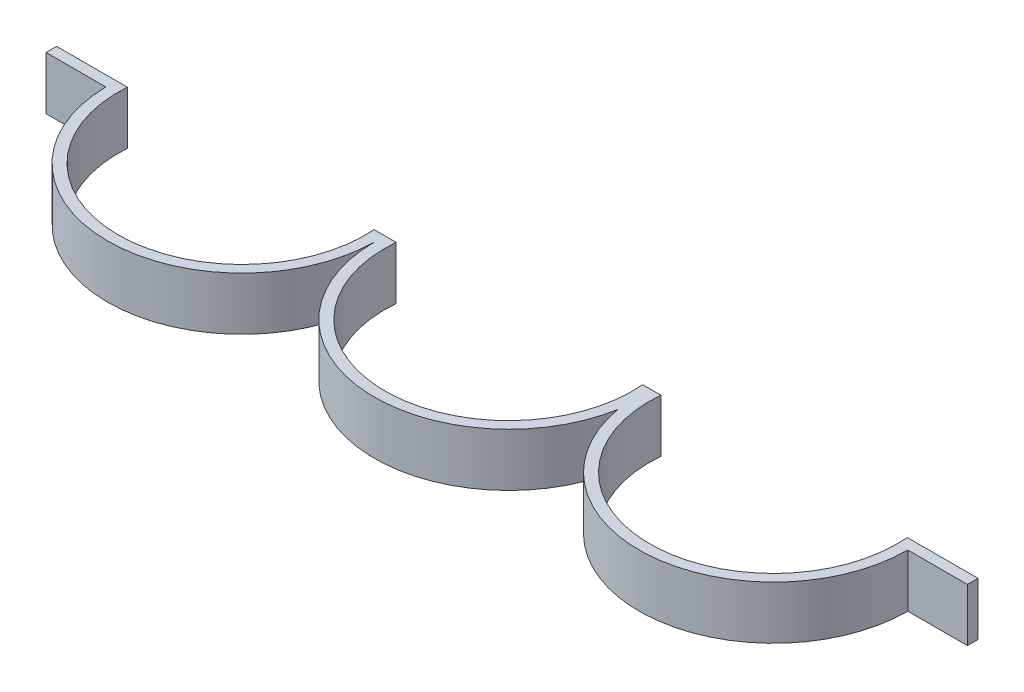
SolidWorks part; units mm, degrees
ref_plane "前视基准面" through (0, 0, 0) normal (0, 0, 1) x (1, 0, 0)
ref_plane "上视基准面" through (0, 0, 0) normal (0, 1, 0) x (1, 0, 0)
ref_plane "右视基准面" through (0, 0, 0) normal (1, 0, 0) x (0, 0, -1)
sketch "草图3" plane through (0, 0, 0) normal (0, 1, 0) x (1, 0, 0)
  line L0 (-227.9856, 0) -> (-261.8173, 0)
  line L1 (-261.8173, 0) -> (-261.8173, 6)
  line L2 (225.761, 0) -> (259.5034, 0)
  line L3 (259.5034, 0) -> (259.5034, 6)
  line L4 (-261.8173, 6) -> (-221.8173, 6)
  line L5 (-82.1683, 6) -> (-69.7424, 6)
  line L6 (69.7424, 6) -> (80.0186, 6)
  line L7 (219.5034, 6) -> (259.5034, 6)
  arc A0 (-76, 0) -> (74.8805, -12.9966) centre (0, 0) ccw
  arc A1 (-76, 0) -> (-227.9856, 0) centre (-151.9928, 1.0468) cw
  arc A2 (74.8805, -12.9966) -> (225.761, 0) centre (149.761, 0) ccw
  arc A3 (-221.8173, 6) -> (-82.1683, 6) centre (-151.9928, 1.0468) ccw
  arc A4 (-69.7424, 6) -> (69.7424, 6) centre (0, 0) ccw
  arc A5 (80.0186, 6) -> (219.5034, 6) centre (149.761, 0) ccw
  dimension "D1" = 76
  dimension "D2" = 76
  dimension "D3" = 76
  dimension "D6" = 70
  dimension "D7" = 70
  dimension "D8" = 70
  dimension "D4" = 6
  dimension "D5" = 6
  dimension "D9" = 40
  dimension "D10" = 40
extrude "凸台-拉伸1" add sketch "草图3" along normal blind 30
